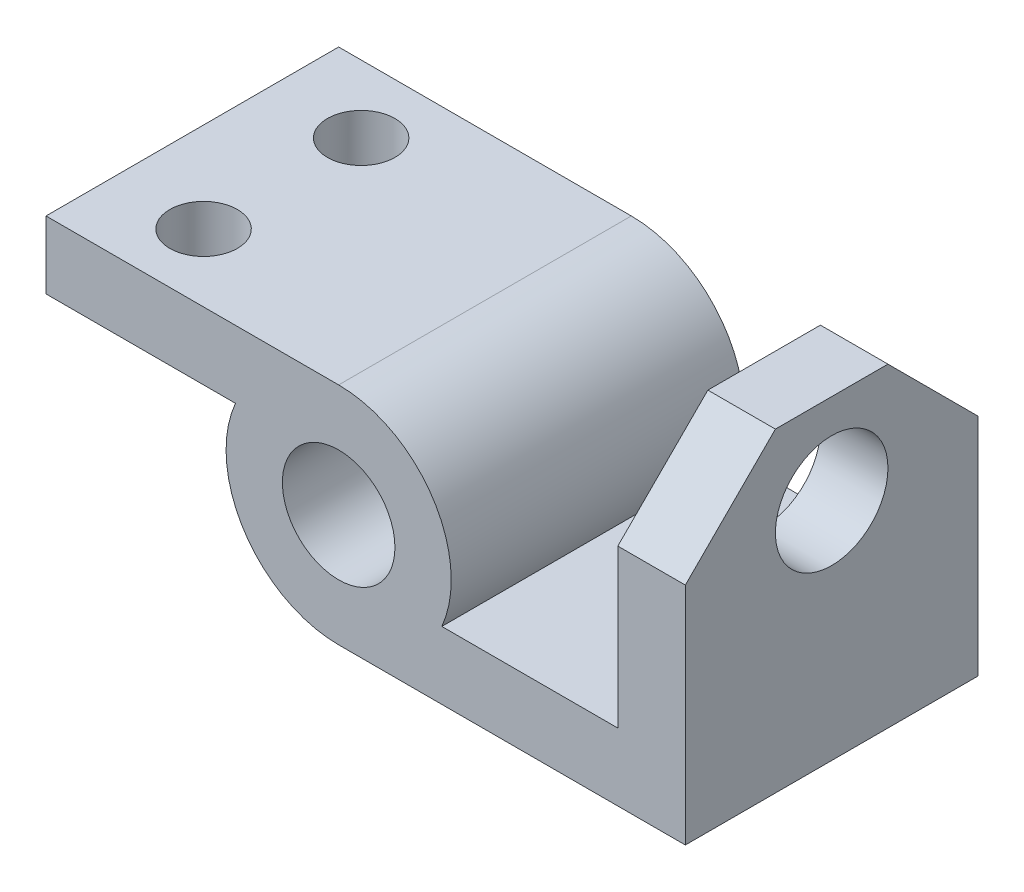
SolidWorks part; units mm, degrees
ref_plane "Front Plane" through (0, 0, 0) normal (0, 0, 1) x (1, 0, 0)
ref_plane "Top Plane" through (0, 0, 0) normal (0, 1, 0) x (1, 0, 0)
ref_plane "Right Plane" through (0, 0, 0) normal (1, 0, 0) x (0, 0, -1)
sketch "Sketch1" plane through (0, 0, 0) normal (0, 0, 1) x (1, 0, 0)
  circle A0 centre (0, 0) radius 31.75
  dimension "D1" = 63.5
extrude "Boss-Extrude1" add sketch "Sketch1" against normal blind 82.55 contours A0
sketch "Sketch3" plane through (0, 0, 0) normal (0, 0, 1) x (1, 0, 0)
  circle A0 centre (0, 0) radius 15.875
  dimension "D1" = 31.75
ref_plane "Plane1" through (31.75, 0, 0) normal (1, 0, 0) x (0, 0, -1)
sketch "Sketch4" plane through (31.75, 0, 0) normal (1, 0, 0) x (0, 0, -1)
  line L0 (0, -31.75) -> (0, -12.7)
  line L1 (0, 31.75) -> (0, -31.75) construction
  line L2 (0, -12.7) -> (82.55, -12.7)
  line L3 (82.55, -31.75) -> (82.55, 31.75) construction
  line L4 (82.55, -12.7) -> (82.55, -31.75)
  line L5 (82.55, -31.75) -> (0, -31.75)
  dimension "D1" = 19.05
extrude "Boss-Extrude2" add sketch "Sketch4" along normal blind 46.99 and the other way blind 31.75
ref_plane "Plane2" through (78.74, 0, 0) normal (1, 0, 0) x (0, 0, -1)
sketch "Sketch5" plane through (78.74, 0, 0) normal (1, 0, 0) x (0, 0, -1)
  line L0 (0, -31.75) -> (0, 57.15)
  line L1 (0, -31.75) -> (82.55, -31.75)
  line L2 (82.55, -31.75) -> (82.55, 57.15)
  line L3 (82.55, 57.15) -> (0, 57.15)
  line L4 (82.55, 31.75) -> (0, 31.75) construction
  circle A0 centre (41.275, 31.75) radius 15.875
  dimension "D2" = 31.75
  dimension "D1" = 88.9
extrude "Boss-Extrude3" add sketch "Sketch5" along normal blind 19.05
chamfer "Chamfer1" distance 25.4 angle 45 2 edges at (88.265, 57.15, -82.55) (88.265, 57.15, 0)
ref_plane "Plane4" through (-31.75, 0, 0) normal (1, 0, 0) x (0, 0, -1)
sketch "Sketch8" plane through (-31.75, 0, 0) normal (1, 0, 0) x (0, 0, -1)
  line L0 (82.55, 31.75) -> (0, 31.75)
  line L1 (0, 31.75) -> (0, 12.7)
  line L2 (0, 31.75) -> (0, -31.75) construction
  line L3 (0, 12.7) -> (82.55, 12.7)
  line L4 (82.55, -31.75) -> (82.55, 31.75) construction
  line L5 (82.55, 12.7) -> (82.55, 31.75)
  dimension "D1" = 19.05
extrude "Boss-Extrude4" add sketch "Sketch8" along normal blind 31.75 and the other way blind 50.8
extrude "Cut-Extrude2" cut sketch "Sketch3" against normal blind 163.576 contours A0
ref_plane "Plane5" through (0, 31.75, 0) normal (0, 1, 0) x (1, 0, 0)
sketch "Sketch9" plane through (0, 31.75, 0) normal (0, 1, 0) x (1, 0, 0)
  line L0 (-82.55, 41.275) -> (-31.75, 41.275) construction
  line L1 (-82.55, 82.55) -> (-82.55, 0) construction
  line L2 (-31.75, -45.4025) -> (-31.75, 45.4025) construction
  circle A0 centre (-57.15, 63.5) radius 9.525
  circle A1 centre (-57.15, 19.05) radius 9.525
  dimension "D1" = 19.05
  dimension "D2" = 19.05
  dimension "D3" = 25.4
extrude "Cut-Extrude3" cut sketch "Sketch9" against normal blind 163.576
